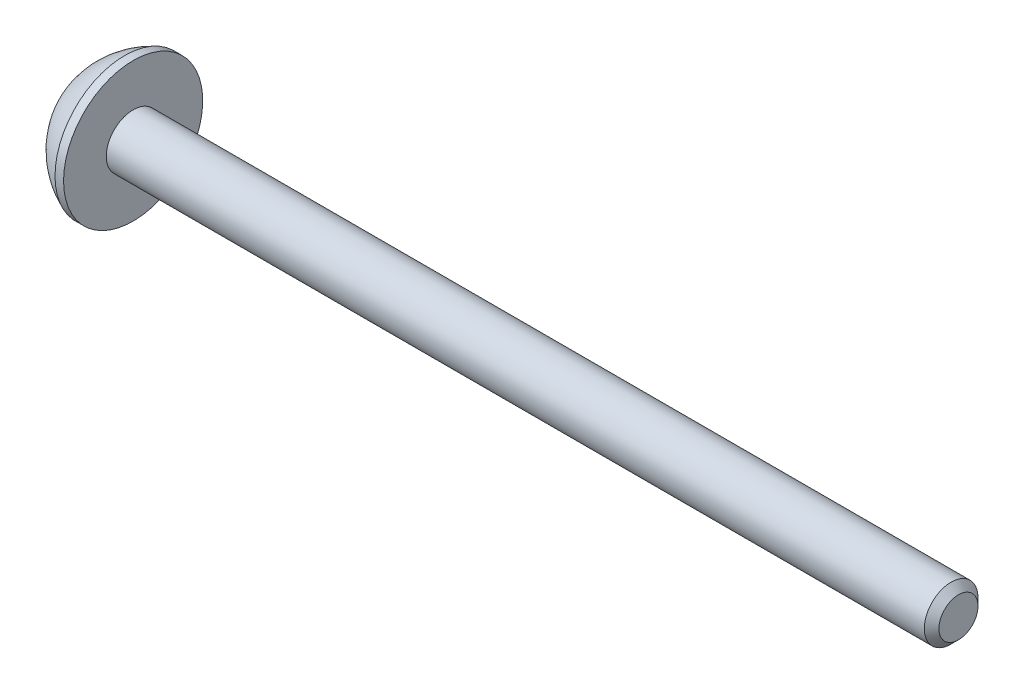
SolidWorks part; units mm, degrees
ref_plane "Front Plane" through (0, 0, 0) normal (0, 0, 1) x (1, 0, 0)
ref_plane "Top Plane" through (0, 0, 0) normal (0, 1, 0) x (1, 0, 0)
ref_plane "Right Plane" through (0, 0, 0) normal (1, 0, 0) x (0, 0, -1)
sketch "Sketch1" plane through (0, 0, 0) normal (0, 0, 1) x (1, 0, 0)
  line L0 (-12.4802, 0) -> (27.75, 0) construction
  line L1 (-12.4802, 2.85) -> (-12.4802, -2.85)
  line L2 (-12.4802, 2.85) -> (-12.8302, 2.85)
  line L3 (-12.8302, 2.85) -> (-12.8302, -2.85)
  line L4 (-12.8302, -2.85) -> (-12.4802, -2.85)
  line L5 (-14.4802, 0) -> (24.8198, 0)
  line L6 (-14.4802, 1.4) -> (-14.4802, -1.4)
  line L8 (-12.4802, 1.1) -> (21.0198, 1.1)
  line L9 (21.0198, 1.1) -> (21.0198, -1.1)
  line L10 (21.0198, -1.1) -> (-12.4802, -1.1)
  line L11 (21.0198, 1.1) -> (21.3198, 0.8)
  line L12 (21.3198, 0.8) -> (21.3198, -0.8)
  line L13 (21.3198, -0.8) -> (21.0198, -1.1)
  arc A0 (-12.8302, 2.85) -> (-14.4802, 1.4) centre (-11.566, -0.2523) ccw
  arc A1 (-14.4802, -1.4) -> (-12.8302, -2.85) centre (-11.566, 0.2523) ccw
  dimension "D13" = 3.35
  dimension "D14" = 3.35
  dimension "D1" = 33.5
  dimension "D2" = 0.3
  dimension "D3" = 1.1
  dimension "D4" = 1.1
  dimension "D5" = 45
  dimension "D6" = 45
  dimension "D7" = 0.35
  dimension "D8" = 1.65
  dimension "D9" = 1.4
  dimension "D10" = 1.4
  dimension "D11" = 2.85
  dimension "D12" = 2.85
revolve "Revolve1" add sketch "Sketch1" angle 360 about L0
sketch "Sketch2" plane through (-14.4802, 0, 0) normal (-1, 0, 0) x (0, 0, 1)
  line L1 (0, 1.1547) -> (-1, 0.5774)
  line L2 (-1, 0.5774) -> (-1, -0.5774)
  line L3 (-1, -0.5774) -> (0, -1.1547)
  line L4 (0, -1.1547) -> (1, -0.5774)
  line L5 (1, -0.5774) -> (1, 0.5774)
  line L6 (1, 0.5774) -> (0, 1.1547)
  circle A0 centre (0, 0) radius 1 construction
  dimension "D1" = 2
extrude "Cut-Extrude1" cut sketch "Sketch2" against normal blind 1
scale "Scale1" bodies to scale 102 scale about centroid uniform scaling yes scale factor 2
